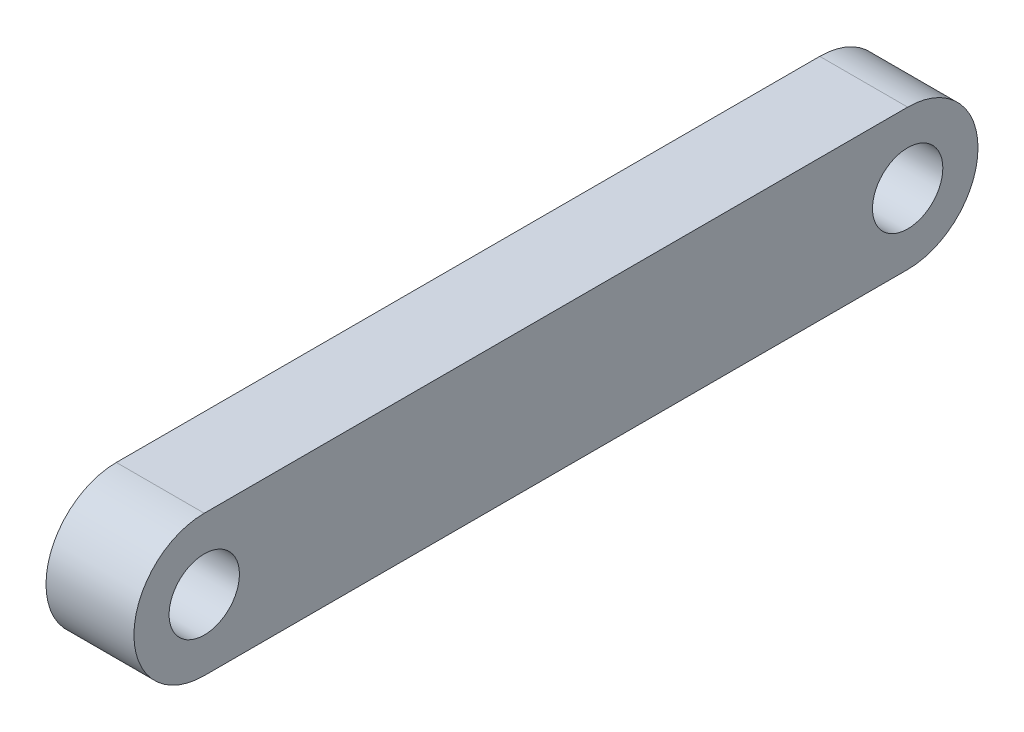
SolidWorks part; units mm, degrees
material "普通碳钢"
ref_plane "前视基准面" through (0, 0, 0) normal (0, 0, 1) x (1, 0, 0)
ref_plane "上视基准面" through (0, 0, 0) normal (0, 1, 0) x (1, 0, 0)
ref_plane "右视基准面" through (0, 0, 0) normal (1, 0, 0) x (0, 0, -1)
sketch "草图1" plane through (0, 0, 0) normal (1, 0, 0) x (0, 0, -1)
  line L0 (-40, 8) -> (40, 8)
  line L1 (-40, -8) -> (40, -8)
  line L2 (0, 0) -> (0, 27.9648) construction
  line L3 (40, 0) -> (0, 0) construction
  line L4 (0, 0) -> (-40, 0) construction
  circle A0 centre (40, 0) radius 4
  arc A1 (-40, -8) -> (-40, 8) centre (-40, 0) cw
  circle A2 centre (-40, 0) radius 4
  arc A3 (40, -8) -> (40, 8) centre (40, 0) ccw
  point P4 (0, 0)
  point P6 (0, -10)
  point P7 (0, 0)
  point P14 (0, 10)
  dimension "D1" = 8
  dimension "D2" = 8
  dimension "D4" = 8
  dimension "D3" = 40
  dimension "D5" = 40
extrude "凸台-拉伸1" add sketch "草图1" along normal blind 10
